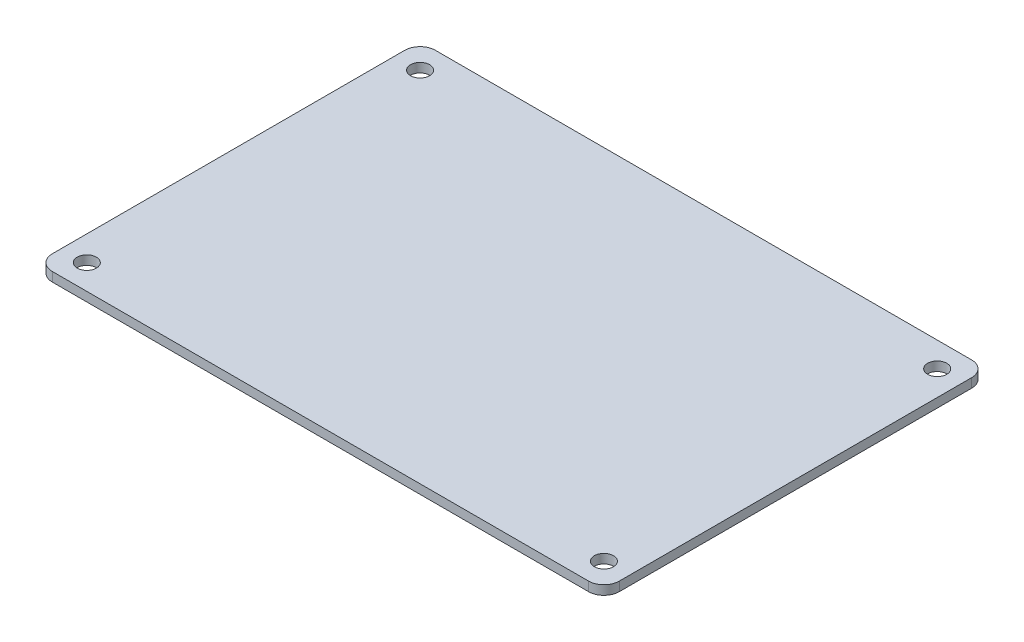
SolidWorks part; units mm, degrees
ref_plane "Front Plane" through (0, 0, 0) normal (0, 0, 1) x (1, 0, 0)
ref_plane "Top Plane" through (0, 0, 0) normal (0, 1, 0) x (1, 0, 0)
ref_plane "Right Plane" through (0, 0, 0) normal (1, 0, 0) x (0, 0, -1)
sketch "Sketch1" plane through (0, 0, 0) normal (0, 1, 0) x (1, 0, 0)
  line L1 (2.54, 0) -> (91.44, 0)
  line L2 (0, -2.54) -> (0, -60.96)
  line L3 (2.54, -63.5) -> (91.44, -63.5)
  line L4 (93.98, -2.54) -> (93.98, -60.96)
  arc A0 (2.54, -63.5) -> (0, -60.96) centre (2.54, -60.96) cw
  arc A1 (93.98, -60.96) -> (91.44, -63.5) centre (91.44, -60.96) cw
  arc A2 (91.44, 0) -> (93.98, -2.54) centre (91.44, -2.54) cw
  arc A3 (2.54, 0) -> (0, -2.54) centre (2.54, -2.54) ccw
  point P7 (0, -63.5)
  point P10 (93.98, -63.5)
  point P13 (93.98, 0)
  point P16 (0, 0)
  dimension "D3" = 2.54
  dimension "D1" = 63.5
  dimension "D2" = 93.98
extrude "Boss-Extrude1" add sketch "Sketch1" along normal blind 1.524 contours L1 A2 L4 A1 L3 A0 L2 A3
sketch "Sketch2" plane through (0, 1.524, 0) normal (0, 1, 0) x (1, 0, 0)
  line L0 (2.54, 0) -> (91.44, 0) construction
  line L1 (0, -2.54) -> (0, -60.96) construction
  line L2 (46.99, 0) -> (46.99, -63.5) construction
  line L3 (2.54, -63.5) -> (91.44, -63.5) construction
  line L4 (0, -31.75) -> (93.98, -31.75) construction
  line L5 (93.98, -2.54) -> (93.98, -60.96) construction
  circle A0 centre (4.1275, -4.1275) radius 1.5875
  circle A1 centre (89.8525, -4.1275) radius 1.5875
  circle A2 centre (4.1275, -59.3725) radius 1.5875
  circle A3 centre (89.8525, -59.3725) radius 1.5875
  dimension "D1" = 3.175
  dimension "D2" = 4.1275
  dimension "D3" = 4.1275
extrude "Cut-Extrude1" cut sketch "Sketch2" against normal through all
sketch "Sketch3" plane through (0, 1.524, 0) normal (0, 1, 0) x (1, 0, 0)
  line L0 (46.99, 0) -> (46.99, -63.5) construction
  line L1 (2.54, 0) -> (91.44, 0) construction
  line L2 (2.54, -63.5) -> (91.44, -63.5) construction
